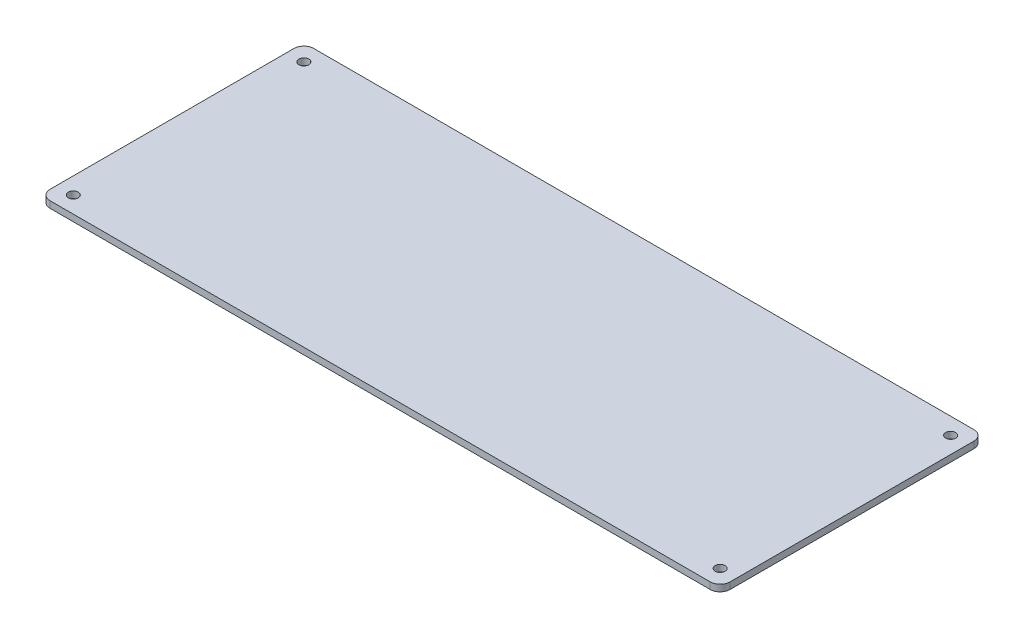
SolidWorks part; units mm, degrees
ref_plane "Front Plane" through (0, 0, 0) normal (0, 0, 1) x (1, 0, 0)
ref_plane "Top Plane" through (0, 0, 0) normal (0, 1, 0) x (1, 0, 0)
ref_plane "Right Plane" through (0, 0, 0) normal (1, 0, 0) x (0, 0, -1)
sketch "Sketch1" plane through (0, 0, 0) normal (0, 1, 0) x (1, 0, 0)
  line L5 (-102.5, -39.75) -> (102.5, -39.75)
  line L6 (-102.5, -39.75) -> (-102.5, 39.75)
  line L7 (-102.5, 39.75) -> (102.5, 39.75)
  line L8 (102.5, -39.75) -> (102.5, 39.75)
  line L9 (-102.5, -39.75) -> (102.5, 39.75) construction
  line L10 (-102.5, 39.75) -> (102.5, -39.75) construction
  point P0 (0, 0)
  dimension "D1" = 205
  dimension "D2" = 79.5
extrude "Boss-Extrude1" add sketch "Sketch1" along normal blind 2
sketch "Sketch2" plane through (0, 2, 0) normal (0, 1, 0) x (1, 0, 0)
  line L0 (102.5, -39.75) -> (102.5, 39.75) construction
  line L1 (102.5, 39.75) -> (-102.5, 39.75) construction
  line L2 (-102.5, -39.75) -> (102.5, -39.75) construction
  line L3 (-102.5, 39.75) -> (-102.5, -39.75) construction
  circle A0 centre (-97.5, 34.75) radius 1.5
  circle A1 centre (-97.5, -34.75) radius 1.5
  circle A2 centre (97.5, -34.75) radius 1.5
  circle A3 centre (97.5, 34.75) radius 1.5
  point P0 (97.5, 34.75)
  point P1 (97.5, -34.75)
  point P2 (-97.5, -34.75)
  point P3 (-97.5, 34.75)
  dimension "D1" = 5
  dimension "D2" = 5
  dimension "D3" = 5
  dimension "D4" = 5
extrude "Cut-Extrude1" cut sketch "Sketch2" against normal blind 2
fillet "Fillet1" radius 3 1 edges at (-102.5, 1, 39.75)
fillet "Fillet3" radius 3 1 edges at (102.5, 1, 39.75)
fillet "Fillet4" radius 3 1 edges at (102.5, 1, -39.75)
fillet "Fillet5" radius 3 1 edges at (-102.5, 1, -39.75)
